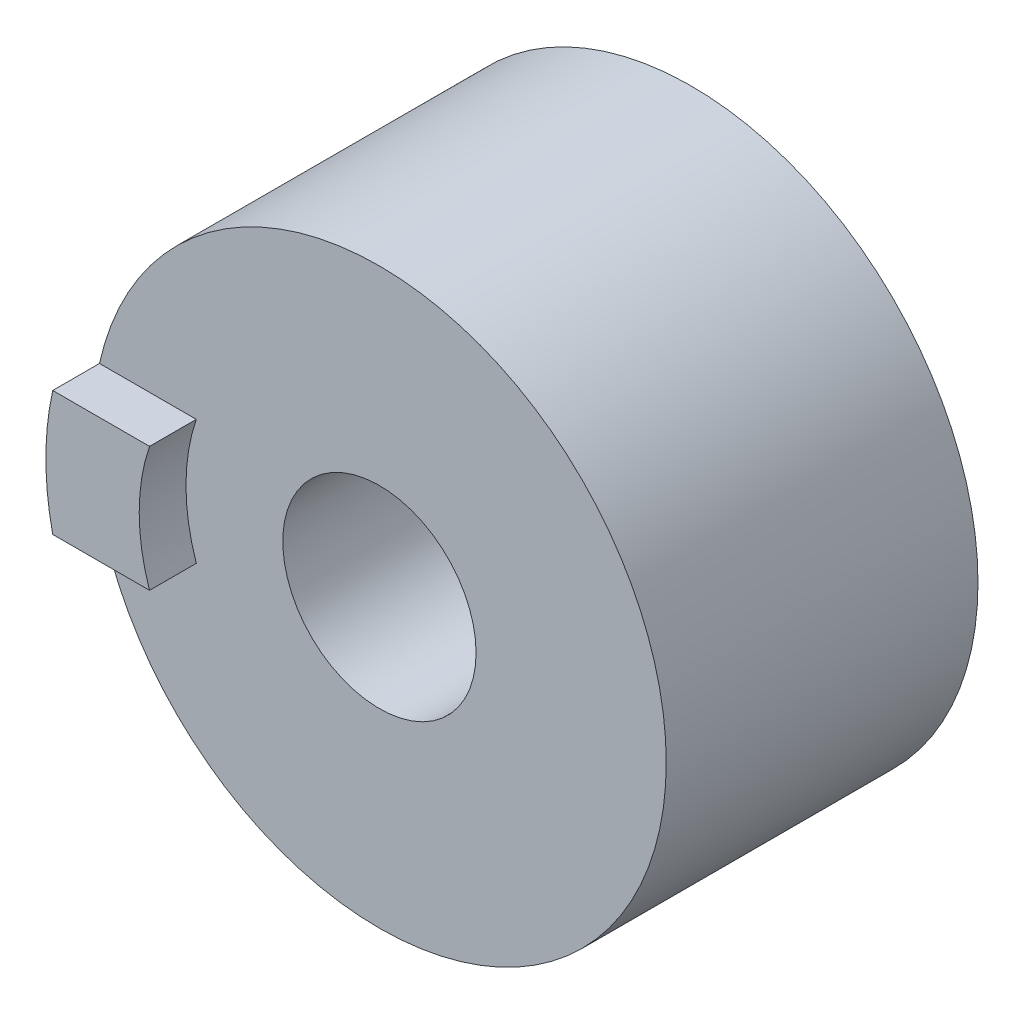
SolidWorks part; units mm, degrees
ref_plane "Front Plane" through (0, 0, 0) normal (0, 0, 1) x (1, 0, 0)
ref_plane "Top Plane" through (0, 0, 0) normal (0, 1, 0) x (1, 0, 0)
ref_plane "Right Plane" through (0, 0, 0) normal (1, 0, 0) x (0, 0, -1)
sketch "Sketch1" plane through (0, 0, 0) normal (0, 1, 0) x (1, 0, 0)
  line L0 (0, -2) -> (3.05, 0)
  line L1 (0, 0) -> (4.6, 0)
  line L2 (0, 0) -> (0, -7)
  line L3 (0, -7) -> (4.6, -7)
  line L4 (4.6, 0) -> (4.6, -7)
  line L5 (3.05, 0) -> (3.05, -7)
  dimension "D1" = 4.6
  dimension "D2" = 7
  dimension "D3" = 2
  dimension "D4" = 1.55
revolve "Revolve1" add sketch "Sketch1" angle 360 about L4
sketch "Sketch2" plane through (0, 0, 7) normal (0, 0, 1) x (1, 0, 0)
  line L2 (0.11, 1) -> (1.6626, 1)
  line L3 (1.6626, -1) -> (0.11, -1)
  arc A0 (0.11, -1) -> (0.11, 1) centre (4.6, 0) cw
  circle A1 centre (4.6, 0) radius 4.6 construction
  arc A3 (1.4971, 0) -> (1.6626, -1) centre (4.6, 0) ccw
  arc A4 (1.4971, 0) -> (1.6626, 1) centre (4.6, 0) cw
  dimension "D1" = 1
  dimension "D2" = 1
extrude "Boss-Extrude1" add sketch "Sketch2" along normal blind 0.75
